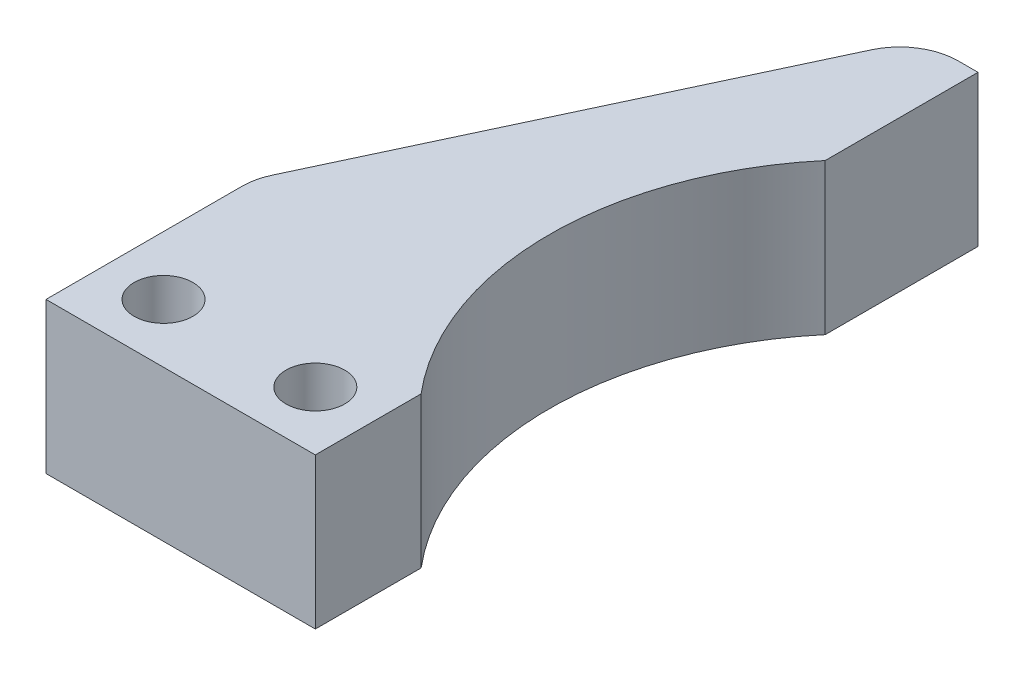
SolidWorks part; units mm, degrees
ref_plane "Front Plane" through (0, 0, 0) normal (0, 0, 1) x (1, 0, 0)
ref_plane "Top Plane" through (0, 0, 0) normal (0, 1, 0) x (1, 0, 0)
ref_plane "Right Plane" through (0, 0, 0) normal (1, 0, 0) x (0, 0, -1)
sketch "Sketch1" plane through (0, 0, 0) normal (0, 1, 0) x (1, 0, 0)
  line L0 (-13.75, -5.4) -> (0, -5.4)
  line L1 (-13.75, -5.4) -> (-13.75, 4.6)
  line L2 (-13.4671, 5.8717) -> (-3.7171, 26.7029)
  line L3 (-1, 28.4312) -> (0, 28.4312)
  line L4 (0, 28.4312) -> (0, 20.6312)
  line L5 (0, -5.4) -> (0, 0)
  line L6 (-6.875, -18.3439) -> (-6.875, 41.8929) construction
  line L7 (0, 28.4312) -> (3.85, 28.4312)
  line L8 (3.85, 28.4312) -> (3.85, 20.6312)
  line L9 (3.85, 20.6312) -> (0, 20.6312)
  arc A0 (0, 0) -> (0, 20.6312) centre (12.2306, 10.3156) cw
  arc A1 (-3.7171, 26.7029) -> (-1, 28.4312) centre (-1, 25.4312) cw
  arc A2 (-13.75, 4.6) -> (-13.4671, 5.8717) centre (-10.75, 4.6) cw
  circle A3 centre (-10.75, -2.4) radius 1.5
  circle A5 centre (-3, -2.4) radius 1.5
  dimension "D1" = 3
  dimension "D2" = 3
  dimension "D6" = 16
  dimension "D10" = 3
  dimension "D12" = 3
  dimension "D3" = 13.75
  dimension "D4" = 5.4
  dimension "D5" = 10
  dimension "D7" = 23
  dimension "D8" = 7.8
  dimension "D9" = 1
  dimension "D11" = 3
  dimension "D13" = 3.85
  dimension "D14" = 7.75
extrude "Boss-Extrude3" add sketch "Sketch1" along normal mid plane 7.7 contours L6 L0 L5 A0 L4 L3 A1 L2 A5 | L0 L6 L2 A2 L1 A3
